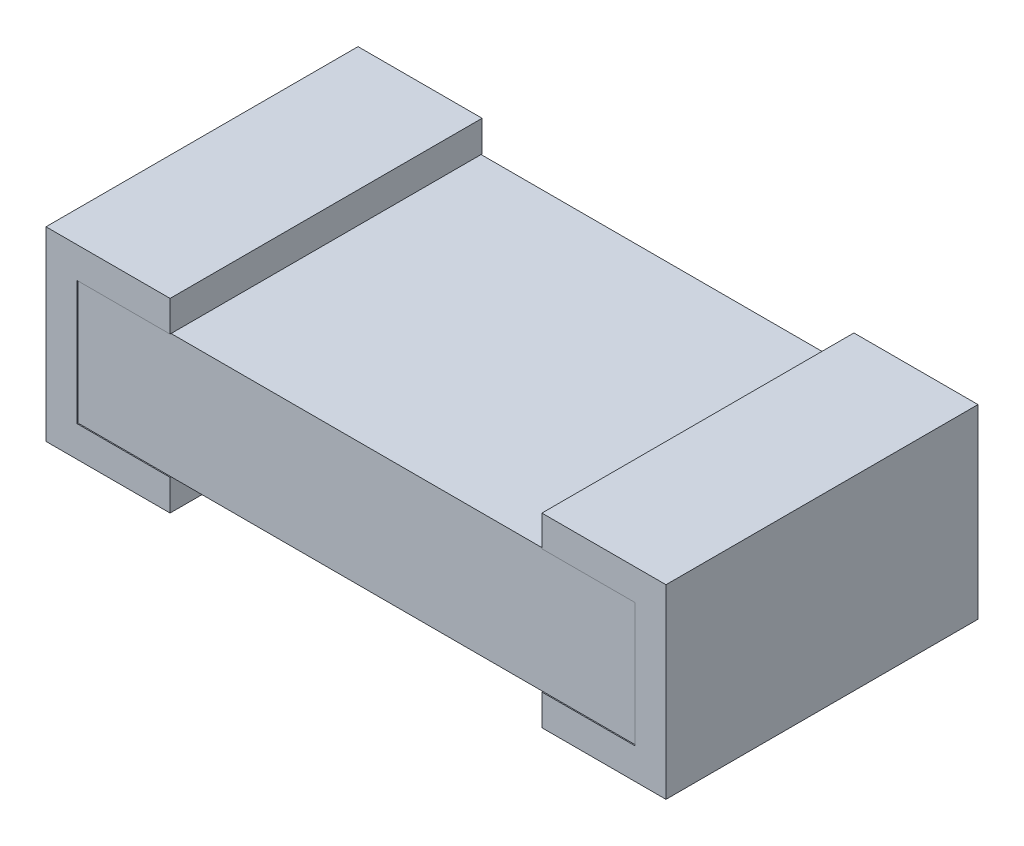
SolidWorks part; units mm, degrees
ref_plane "Plano frontal" through (0, 0, 0) normal (0, 0, 1) x (1, 0, 0)
ref_plane "Plano superior" through (0, 0, 0) normal (0, 1, 0) x (1, 0, 0)
ref_plane "Plano direito" through (0, 0, 0) normal (1, 0, 0) x (0, 0, -1)
sketch "Esboço1" plane through (0, 0, 0) normal (0, 0, 1) x (1, 0, 0)
  line L1 (-0.686, -0.1525) -> (0.686, -0.1525)
  line L2 (-0.686, -0.1525) -> (-0.686, 0.1525)
  line L3 (-0.686, 0.1525) -> (0.686, 0.1525)
  line L4 (0.686, -0.1525) -> (0.686, 0.1525)
  line L5 (-0.686, -0.1525) -> (0.686, 0.1525) construction
  line L6 (-0.686, 0.1525) -> (0.686, -0.1525) construction
  point P0 (0, 0)
  dimension "D1" = 1.372
  dimension "D2" = 0.305
extrude "Ressalto-extrusão1" add sketch "Esboço1" along normal mid plane 0.762
sketch "Esboço2" plane through (0, 0, 0) normal (0, 0, 1) x (1, 0, 0)
  line L0 (-0.457, 0.1525) -> (-0.686, 0.1525)
  line L1 (0.686, 0.1525) -> (-0.686, 0.1525) construction
  line L2 (-0.686, 0.1525) -> (-0.686, -0.1525)
  line L3 (-0.686, -0.1525) -> (-0.457, -0.1525)
  line L4 (-0.686, -0.1525) -> (0.686, -0.1525) construction
  line L5 (-0.457, -0.1525) -> (-0.457, -0.2285)
  line L6 (-0.457, -0.2285) -> (-0.762, -0.2285)
  line L7 (-0.762, -0.2285) -> (-0.762, 0.2285)
  line L8 (-0.762, 0.2285) -> (-0.457, 0.2285)
  line L9 (-0.457, 0.2285) -> (-0.457, 0.1525)
  dimension "D1" = 0.076
  dimension "D2" = 0.076
  dimension "D3" = 0.076
  dimension "D4" = 0.305
  dimension "D5" = 0.305
extrude "Ressalto-extrusão2" add sketch "Esboço2" along normal mid plane 0.767
mirror "Espelhar1" about plane through (0, 0, 0) normal (1, 0, 0) of "Ressalto-extrusão2"
